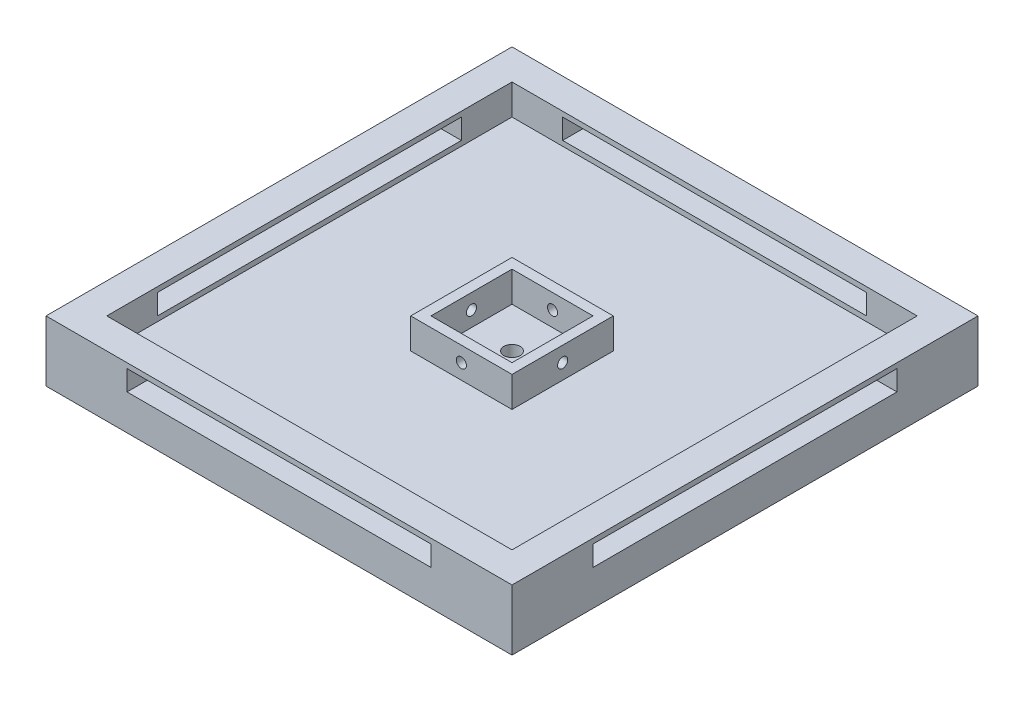
SolidWorks part; units mm, degrees
ref_plane "Front Plane" through (0, 0, 0) normal (0, 0, 1) x (1, 0, 0)
ref_plane "Top Plane" through (0, 0, 0) normal (0, 1, 0) x (1, 0, 0)
ref_plane "Right Plane" through (0, 0, 0) normal (1, 0, 0) x (0, 0, -1)
sketch "Sketch1" plane through (0, 0, 0) normal (0, 1, 0) x (1, 0, 0)
  line L1 (0, 0) -> (-40, 0)
  line L2 (0, 0) -> (0, -40)
  line L3 (0, -40) -> (-40, -40)
  line L4 (-40, 0) -> (-40, -40)
  dimension "D1" = 40
  dimension "D2" = 40
extrude "Boss-Extrude1" add sketch "Sketch1" along normal blind 3
sketch "Sketch2" plane through (0, 0, 0) normal (1, 0, 0) x (0, 0, -1)
  line L1 (0, 0) -> (-40, 0)
  line L2 (0, 0) -> (0, 6)
  line L3 (0, 6) -> (-40, 6)
  line L4 (-40, 0) -> (-40, 6)
  dimension "D1" = 6
extrude "Boss-Extrude2" add sketch "Sketch2" along normal blind 3 separate body
sketch "Sketch4" plane through (0, 0, 40) normal (0, 0, 1) x (1, 0, 0)
  line L1 (3, 0) -> (-40, 0)
  line L2 (3, 0) -> (3, 6)
  line L3 (3, 6) -> (-40, 6)
  line L4 (-40, 0) -> (-40, 6)
extrude "Boss-Extrude3" add sketch "Sketch4" along normal blind 3
sketch "Sketch5" plane through (0, 0, 0) normal (0, 0, -1) x (-1, 0, 0)
  line L1 (-3, 0) -> (40, 0)
  line L2 (-3, 0) -> (-3, 6)
  line L3 (-3, 6) -> (40, 6)
  line L4 (40, 0) -> (40, 6)
extrude "Boss-Extrude4" add sketch "Sketch5" along normal blind 3
sketch "Sketch6" plane through (-40, 0, 0) normal (-1, 0, 0) x (0, 0, 1)
  line L1 (-3, 0) -> (43, 0)
  line L2 (-3, 0) -> (-3, 6)
  line L3 (-3, 6) -> (43, 6)
  line L4 (43, 0) -> (43, 6)
extrude "Boss-Extrude5" add sketch "Sketch6" along normal blind 3
sketch "Sketch7" plane through (0, 0, 0) normal (-1, 0, 0) x (0, 0, 1)
  line L0 (0, 6) -> (40, 6) construction
  line L1 (0, 3) -> (0, 6) construction
  line L3 (35, 5.5) -> (5, 5.5)
  line L4 (35, 5.5) -> (35, 3.5)
  line L5 (35, 3.5) -> (5, 3.5)
  line L6 (5, 5.5) -> (5, 3.5)
  line L7 (35, 5.5) -> (5, 3.5) construction
  line L8 (35, 3.5) -> (5, 5.5) construction
  point P0 (20, 6)
  point P1 (0, 4.5)
  point P4 (20, 4.5)
  point P7 (20, 4.5)
  dimension "D1" = 2
  dimension "D2" = 30
extrude "Cut-Extrude1" cut sketch "Sketch7" against normal blind 3
ref_plane "Plane1" through (0, 0, 0) normal (0.7071, 0, 0.7071) x (0.7071, 0, -0.7071)
mirror "Mirror1" about plane through (0, 0, 0) normal (0.7071, 0, 0.7071) of "Cut-Extrude1"
ref_plane "Plane2" through (-20, 0, 20) normal (0.7071, 0, -0.7071) x (-0.7071, 0, -0.7071)
mirror "Mirror2" about plane through (-20, 0, 20) normal (0.7071, 0, -0.7071) of "Mirror1", "Cut-Extrude1"
sketch "Sketch8" plane through (0, 3, 0) normal (0, 1, 0) x (1, 0, 0)
  line L0 (0, -40) -> (0, 0) construction
  line L1 (0, 0) -> (-40, 0) construction
  line L3 (-15, -25) -> (-25, -25)
  line L4 (-15, -25) -> (-15, -15)
  line L5 (-15, -15) -> (-25, -15)
  line L6 (-25, -25) -> (-25, -15)
  line L7 (-15, -25) -> (-25, -15) construction
  line L8 (-15, -15) -> (-25, -25) construction
  line L9 (-16.0002, -23.9998) -> (-23.9998, -23.9998)
  line L10 (-16.0002, -23.9998) -> (-16.0002, -16.0002)
  line L11 (-16.0002, -16.0002) -> (-23.9998, -16.0002)
  line L12 (-23.9998, -23.9998) -> (-23.9998, -16.0002)
  line L13 (-16.0002, -23.9998) -> (-23.9998, -16.0002) construction
  line L14 (-16.0002, -16.0002) -> (-23.9998, -23.9998) construction
  point P0 (0, -20)
  point P1 (-20, 0)
  point P4 (-20, -20)
  point P7 (-20, -20)
  point P12 (-20, -20)
  dimension "D1" = 10
  dimension "D2" = 10
extrude "Boss-Extrude6" add sketch "Sketch8" along normal blind 3
sketch "Sketch9" plane through (0, 3, 0) normal (0, 1, 0) x (1, 0, 0)
  circle A0 centre (-20, -20) radius 0.8
extrude "Cut-Extrude2" cut sketch "Sketch9" against normal blind 3
sketch "Sketch10" plane through (-25, 0, 0) normal (-1, 0, 0) x (0, 0, 1)
  line L0 (15, 3) -> (25, 3) construction
  line L1 (15, 6) -> (15, 3) construction
  circle A0 centre (20, 4.5) radius 0.5
  point P0 (20, 3)
  point P1 (15, 4.5)
  point P4 (20, 4.5)
extrude "Cut-Extrude3" cut sketch "Sketch10" against normal blind 10
mirror "Mirror3" about plane through (-20, 0, 20) normal (0.7071, 0, -0.7071) of "Cut-Extrude3"
sketch "Sketch11" plane through (0, 3, 0) normal (0, 1, 0) x (1, 0, 0)
  circle A0 centre (-20, -20) radius 1
  circle A1 centre (-20, -20) radius 0.8
sketch "Sketch12" plane through (-23.9998, 0, 0) normal (1, 0, 0) x (0, 0, -1)
  circle A0 centre (-20, 4.5) radius 0.125
  dimension "D1" = 0.25
